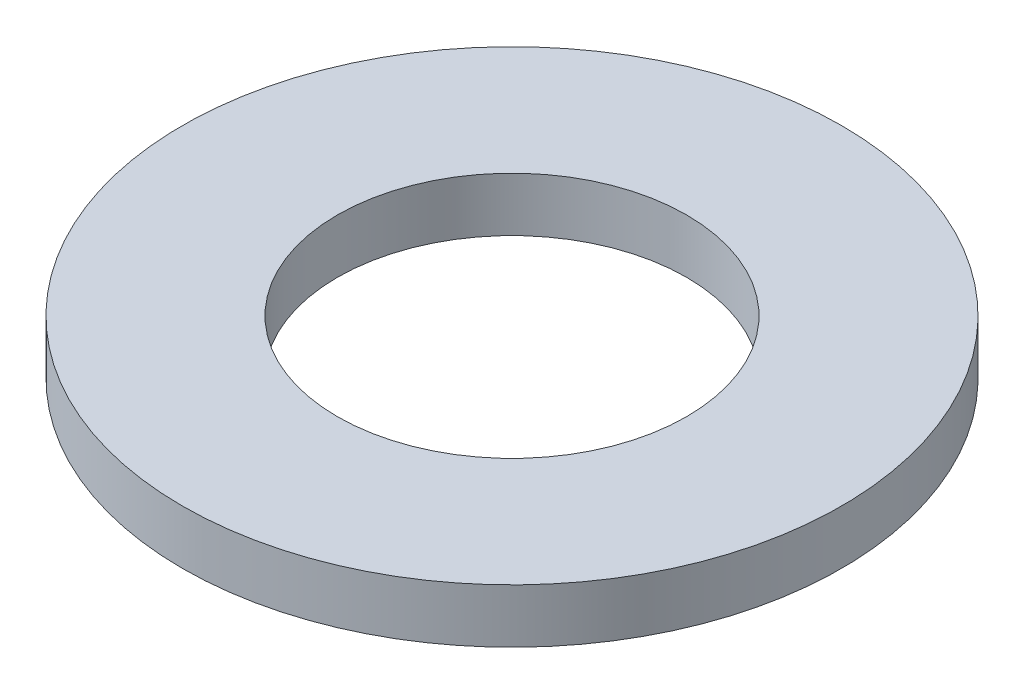
SolidWorks part; units mm, degrees
ref_plane "Front Plane" through (0, 0, 0) normal (0, 0, 1) x (1, 0, 0)
ref_plane "Top Plane" through (0, 0, 0) normal (0, 1, 0) x (1, 0, 0)
ref_plane "Right Plane" through (0, 0, 0) normal (1, 0, 0) x (0, 0, -1)
sketch "Sketch1" plane through (0, 0, 0) normal (0, 1, 0) x (1, 0, 0)
  circle A0 centre (0, 0) radius 6.35
  dimension "OD" = 12.7
extrude "Boss-Extrude1" add sketch "Sketch1" along normal blind 1.0414
sketch "Sketch5" plane through (0, 1.0414, 0) normal (0, 1, 0) x (-1, 0, 0)
  circle A0 centre (0, 0) radius 3.3655
  dimension "ID" = 6.731
extrude "Cut-Extrude1" cut sketch "Sketch5" against normal through all
